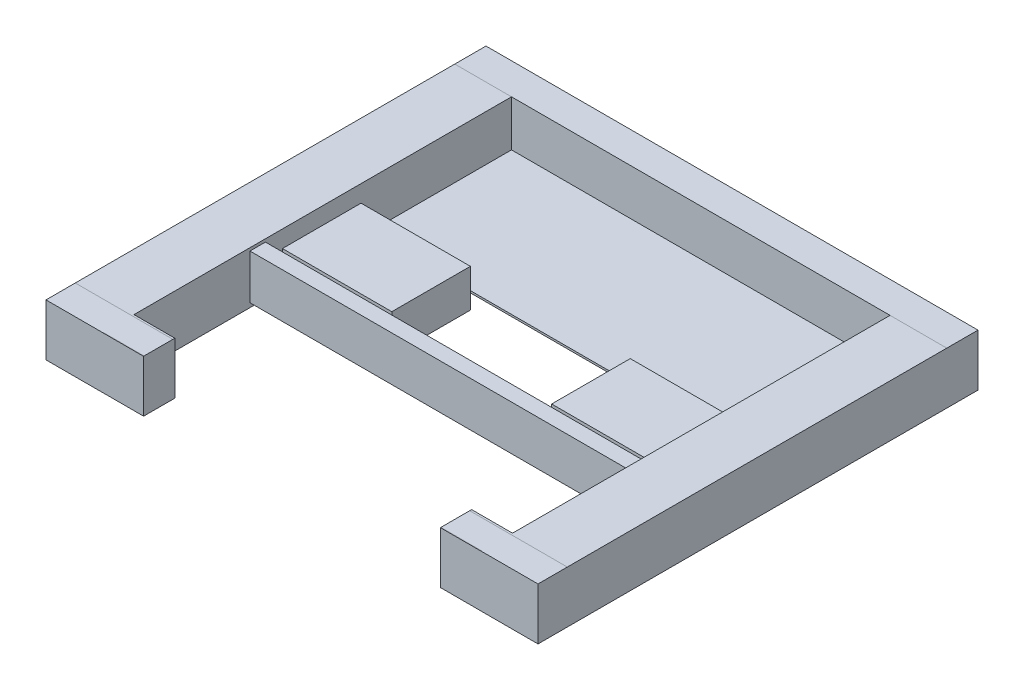
SolidWorks part; units mm, degrees
ref_plane "Front Plane" through (0, 0, 0) normal (0, 0, 1) x (1, 0, 0)
ref_plane "Top Plane" through (0, 0, 0) normal (0, 1, 0) x (1, 0, 0)
ref_plane "Right Plane" through (0, 0, 0) normal (1, 0, 0) x (0, 0, -1)
sketch "Sketch1" plane through (-470.5973, 0, 0) normal (-1, 0, 0) x (0, 0, 1)
  line L0 (375.9827, 96.3326) -> (375.9827, 19.6246) construction
  line L1 (375.9827, 100.2696) -> (375.9827, 15.6876)
  line L2 (328.3577, 100.2696) -> (375.2207, 100.2696) construction
  line L3 (328.3577, 100.2696) -> (375.9827, 100.2696)
  line L4 (375.2207, 15.6876) -> (347.4077, 15.6876) construction
  line L5 (375.9827, 15.6876) -> (347.4077, 15.6876)
  line L6 (-308.1663, 15.4336) -> (-335.9793, 15.4336) construction
  line L7 (-308.1663, 15.4336) -> (-339.9163, 15.4336)
  line L8 (-339.9163, 19.3706) -> (-339.9163, 96.0786) construction
  line L9 (-339.9163, 15.4336) -> (-339.9163, 100.0156)
  line L10 (-335.9793, 100.0156) -> (-289.1163, 100.0156) construction
  line L11 (-339.9163, 100.0156) -> (-289.1163, 100.0156)
  line L12 (-308.1663, 15.4336) -> (347.4077, 15.6876)
  line L13 (-289.1163, 100.0156) -> (328.3577, 100.2696)
extrude "Boss-Extrude1" add sketch "Sketch1" against normal up to surface (92.2881 mm away)
sketch "Sketch2" plane through (-378.3092, 0, 0) normal (1, 0, 0) x (0, 0, -1)
  line L0 (-344.2327, 18.8626) -> (-344.2327, 15.6876) construction
  line L1 (-344.2327, 18.8626) -> (-344.2327, 15.6876)
  line L3 (-325.1827, 100.2696) -> (-375.2207, 100.2696)
  line L4 (-325.1827, 100.2696) -> (-325.1827, 15.6876)
  line L5 (-325.1827, 15.6876) -> (-375.2207, 15.6876)
  line L6 (-375.2207, 100.2696) -> (-375.2207, 15.6876)
  line L8 (289.1163, 100.0156) -> (-328.3577, 100.2696)
  line L9 (-328.3577, 100.2696) -> (-375.9827, 100.2696)
  line L10 (-375.9827, 100.2696) -> (-375.9827, 15.6876)
  line L11 (-375.9827, 15.6876) -> (-347.4077, 15.6876)
  line L12 (-347.4077, 15.6876) -> (308.1663, 15.4336)
  line L13 (308.1663, 15.4336) -> (339.9163, 15.4336)
  line L14 (339.9163, 15.4336) -> (339.9163, 100.0156)
  line L15 (339.9163, 100.0156) -> (289.1163, 100.0156)
  line L16 (289.1163, 100.0156) -> (-328.3577, 100.2696)
  line L17 (-328.3577, 100.2696) -> (-375.9827, 100.2696)
  line L18 (-375.9827, 100.2696) -> (-375.9827, 15.6876)
  line L19 (-375.9827, 15.6876) -> (-347.4077, 15.6876)
  line L20 (-347.4077, 15.6876) -> (308.1663, 15.4336)
  line L21 (308.1663, 15.4336) -> (339.9163, 15.4336)
  line L22 (339.9163, 15.4336) -> (339.9163, 100.0156)
  line L23 (339.9163, 100.0156) -> (289.1163, 100.0156)
  line L26 (-344.2327, 18.8626) -> (-375.2207, 18.8626)
  line L27 (-375.9827, 19.6246) -> (-375.9827, 96.3326)
  line L28 (-375.2207, 97.0946) -> (-325.1827, 97.0946)
  line L29 (-325.1827, 97.0946) -> (-325.1827, 100.2696)
  line L30 (-325.1827, 100.2696) -> (-375.2207, 100.2696)
  line L31 (-379.1577, 96.3326) -> (-379.1577, 19.6246)
  line L32 (-375.2207, 15.6876) -> (-344.2327, 15.6876)
  line L33 (-344.2327, 15.6876) -> (-344.2327, 18.8626)
  line L34 (-344.2327, 18.8626) -> (-375.2207, 18.8626)
  line L35 (-375.9827, 19.6246) -> (-375.9827, 96.3326)
  line L36 (-375.2207, 97.0946) -> (-325.1827, 97.0946)
  line L37 (-325.1827, 97.0946) -> (-325.1827, 100.2696)
  line L38 (-325.1827, 100.2696) -> (-375.2207, 100.2696)
  line L39 (-379.1577, 96.3326) -> (-379.1577, 19.6246)
  line L40 (-375.2207, 15.6876) -> (-344.2327, 15.6876)
  line L41 (-344.2327, 15.6876) -> (-344.2327, 18.8626)
  arc A4 (-375.9827, 19.6246) -> (-375.2207, 18.8626) centre (-375.2207, 19.6246) ccw
  arc A5 (-375.2207, 97.0946) -> (-375.9827, 96.3326) centre (-375.2207, 96.3326) ccw
  arc A6 (-375.2207, 100.2696) -> (-379.1577, 96.3326) centre (-375.2207, 96.3326) ccw
  arc A7 (-379.1577, 19.6246) -> (-375.2207, 15.6876) centre (-375.2207, 19.6246) ccw
  arc A8 (-375.9827, 19.6246) -> (-375.2207, 18.8626) centre (-375.2207, 19.6246) ccw
  arc A9 (-375.2207, 97.0946) -> (-375.9827, 96.3326) centre (-375.2207, 96.3326) ccw
  arc A10 (-375.2207, 100.2696) -> (-379.1577, 96.3326) centre (-375.2207, 96.3326) ccw
  arc A11 (-379.1577, 19.6246) -> (-375.2207, 15.6876) centre (-375.2207, 19.6246) ccw
  line M21 (289.1163, 100.0156) -> (-328.3577, 100.2696)
  line M22 (-328.3577, 100.2696) -> (-375.9827, 100.2696)
  line M23 (-375.9827, 100.2696) -> (-375.9827, 15.6876)
  line M24 (-375.9827, 15.6876) -> (-347.4077, 15.6876)
  dimension "D1" = 0
  dimension "D2" = 0
extrude "Boss-Extrude2" add sketch "Sketch2" along normal up to surface (66.4619 mm away) contours L36 L6 L34 L1 L5 L4 | L6 L36 L4 M21 M22 | L6 A10 L18 A9 | L6 A9 L18 A8 | L1 L34 L6 L5 M24 | A11 L6 A8 M23
ref_plane "Plane1" through (-70.3342, 0, 0) normal (1, 0, 0) x (0, 0, -1)
sketch "Sketch3" plane through (-378.3092, 0, 0) normal (1, 0, 0) x (0, 0, -1)
  line L1 (289.1163, 100.0156) -> (339.9163, 100.0156)
  line L2 (289.1163, 100.0156) -> (289.1163, 15.4336)
  line L3 (289.1163, 15.4336) -> (339.9163, 15.4336)
  line L4 (339.9163, 100.0156) -> (339.9163, 15.4336)
  line L7 (289.1163, 100.0156) -> (-325.1827, 100.2683)
  line L8 (-325.1827, 100.2683) -> (-325.1827, 15.6876)
  line L9 (-325.1827, 15.6876) -> (-347.4077, 15.6876)
  line L10 (-347.4077, 15.6876) -> (308.1663, 15.4336)
  line L11 (308.1663, 15.4336) -> (339.9163, 15.4336)
  line L12 (339.9163, 15.4336) -> (339.9163, 100.0156)
  line L13 (339.9163, 100.0156) -> (289.1163, 100.0156)
  line L14 (289.1163, 100.0156) -> (-325.1827, 100.2683)
  line L15 (-325.1827, 100.2683) -> (-325.1827, 15.6876)
  line L16 (-325.1827, 15.6876) -> (-347.4077, 15.6876)
  line L17 (-347.4077, 15.6876) -> (308.1663, 15.4336)
  line L18 (308.1663, 15.4336) -> (339.9163, 15.4336)
  line L19 (339.9163, 15.4336) -> (339.9163, 100.0156)
  line L20 (339.9163, 100.0156) -> (289.1163, 100.0156)
  line L22 (336.7413, 96.0786) -> (336.7413, 19.3706)
  line L23 (335.9793, 18.6086) -> (308.1663, 18.6086)
  line L24 (308.1663, 18.6086) -> (308.1663, 15.4336)
  line L25 (308.1663, 15.4336) -> (335.9793, 15.4336)
  line L26 (339.9163, 19.3706) -> (339.9163, 96.0786)
  line L27 (335.9793, 100.0156) -> (289.1163, 100.0156)
  line L28 (289.1163, 100.0156) -> (289.1163, 96.8406)
  line L29 (289.1163, 96.8406) -> (335.9793, 96.8406)
  line L30 (336.7413, 96.0786) -> (336.7413, 19.3706)
  line L31 (335.9793, 18.6086) -> (308.1663, 18.6086)
  line L32 (308.1663, 18.6086) -> (308.1663, 15.4336)
  line L33 (308.1663, 15.4336) -> (335.9793, 15.4336)
  line L34 (339.9163, 19.3706) -> (339.9163, 96.0786)
  line L35 (335.9793, 100.0156) -> (289.1163, 100.0156)
  line L36 (289.1163, 100.0156) -> (289.1163, 96.8406)
  line L37 (289.1163, 96.8406) -> (335.9793, 96.8406)
  line L958 (57.3413, 22.0376) -> (336.7413, 22.0376)
  line L959 (336.7413, 22.0376) -> (336.7413, 25.2126)
  line L960 (336.7413, 25.2126) -> (57.3413, 25.2126)
  line L961 (57.3413, 25.2126) -> (57.3413, 22.0376)
  line L962 (57.3413, 22.0376) -> (336.7413, 22.0376)
  line L963 (336.7413, 22.0376) -> (336.7413, 25.2126)
  line L964 (336.7413, 25.2126) -> (57.3413, 25.2126)
  line L965 (57.3413, 25.2126) -> (57.3413, 22.0376)
  arc A4 (335.9793, 18.6086) -> (336.7413, 19.3706) centre (335.9793, 19.3706) ccw
  arc A5 (335.9793, 15.4336) -> (339.9163, 19.3706) centre (335.9793, 19.3706) ccw
  arc A6 (339.9163, 96.0786) -> (335.9793, 100.0156) centre (335.9793, 96.0786) ccw
  arc A7 (336.7413, 96.0786) -> (335.9793, 96.8406) centre (335.9793, 96.0786) ccw
  arc A8 (335.9793, 18.6086) -> (336.7413, 19.3706) centre (335.9793, 19.3706) ccw
  arc A9 (335.9793, 15.4336) -> (339.9163, 19.3706) centre (335.9793, 19.3706) ccw
  arc A10 (339.9163, 96.0786) -> (335.9793, 100.0156) centre (335.9793, 96.0786) ccw
  arc A11 (336.7413, 96.0786) -> (335.9793, 96.8406) centre (335.9793, 96.0786) ccw
  line M23 (-347.4077, 15.6876) -> (308.1663, 15.4336)
  line M24 (308.1663, 15.4336) -> (339.9163, 15.4336)
  line M25 (339.9163, 15.4336) -> (339.9163, 100.0156)
  line M26 (339.9163, 100.0156) -> (289.1163, 100.0156)
  dimension "D1" = 0
  dimension "D2" = 0
  dimension "D3" = 0
extrude "Boss-Extrude3" add sketch "Sketch3" along normal up to surface (307.975 mm away) contours L30 A11 L37 L2 L32 L31 A8 M23 | A11 L30 A8 L31 L32 A9 L19 A10 L20 L2 L37 M24 | A10 M25 M26 | A9 L18 M25 | L30 A11 L37 L2 L964 | L30 L964 L2 L962 | L964 L965 L962 L2
sketch "Sketch4" plane through (-378.3092, 0, 0) normal (1, 0, 0) x (0, 0, -1)
  line L1 (-83.5558, 72.5361) -> (44.3144, 72.5361)
  line L2 (-83.5558, 72.5361) -> (-83.5558, 10.7821)
  line L3 (-83.5558, 10.7821) -> (44.3144, 10.7821)
  line L4 (44.3144, 72.5361) -> (44.3144, 10.7821)
  line L9 (289.1163, 25.2126) -> (289.1163, 100.0156)
  line L10 (289.1163, 100.0156) -> (-325.1827, 100.2683)
  line L11 (-325.1827, 100.2683) -> (-325.1827, 15.6876)
  line L12 (-325.1827, 15.6876) -> (-347.4077, 15.6876)
  line L13 (-347.4077, 15.6876) -> (289.1163, 15.441)
  line L14 (289.1163, 15.441) -> (289.1163, 22.0376)
  line L15 (289.1163, 22.0376) -> (57.3413, 22.0376)
  line L16 (57.3413, 22.0376) -> (57.3413, 25.2126)
  line L17 (57.3413, 25.2126) -> (289.1163, 25.2126)
  line L18 (289.1163, 25.2126) -> (289.1163, 100.0156)
  line L19 (289.1163, 100.0156) -> (-325.1827, 100.2683)
  line L20 (-325.1827, 100.2683) -> (-325.1827, 15.6876)
  line L21 (-325.1827, 15.6876) -> (-347.4077, 15.6876)
  line L22 (-347.4077, 15.6876) -> (289.1163, 15.441)
  line L23 (289.1163, 15.441) -> (289.1163, 22.0376)
  line L24 (289.1163, 22.0376) -> (57.3413, 22.0376)
  line L25 (57.3413, 22.0376) -> (57.3413, 25.2126)
  line L26 (57.3413, 25.2126) -> (289.1163, 25.2126)
  arc A0 (-22.8539, 49.6506) -> (-82.5037, 33.6675) centre (-52.6788, 41.6591) ccw construction
  arc A1 (-82.5037, 33.6675) -> (-22.8539, 49.6506) centre (-52.6788, 41.6591) ccw construction
  arc A2 (-16.3875, 49.6506) -> (43.2623, 33.6675) centre (13.4374, 41.6591) ccw construction
  arc A3 (43.2623, 33.6675) -> (-16.3875, 49.6506) centre (13.4374, 41.6591) ccw construction
  arc A4 (-22.8539, 49.6506) -> (-82.5037, 33.6675) centre (-52.6788, 41.6591) ccw
  arc A5 (-82.5037, 33.6675) -> (-22.8539, 49.6506) centre (-52.6788, 41.6591) ccw
  arc A6 (-16.3875, 49.6506) -> (43.2623, 33.6675) centre (13.4374, 41.6591) ccw
  arc A7 (43.2623, 33.6675) -> (-16.3875, 49.6506) centre (13.4374, 41.6591) ccw
  line M18 (-347.4077, 15.6876) -> (289.1163, 15.441)
  dimension "D1" = 0
extrude "Boss-Extrude4" add sketch "Sketch4" along normal up to surface (177.926 mm away) contours A7 A6 L22 | A4 A5 L22 | A7 L1 A4 A5 A6 M18 | L22 A5 | A6 A5 L3 M18 | L22 A6 | A6 L3 L4 M18 | A5 L2 L3 M18 | A5 A4 L2 M18 | A4 L1 L2 | A7 L4 L1 | A7 A6 L4 M18
sketch "Sketch6" plane through (-378.3092, 0, 0) normal (1, 0, 0) x (0, 0, -1)
  line L1 (-136.4295, 95.4857) -> (-111.2814, 95.4857)
  line L2 (-136.4295, 95.4857) -> (-136.4295, 22.6149)
  line L3 (-136.4295, 22.6149) -> (-111.2814, 22.6149)
  line L4 (-111.2814, 95.4857) -> (-111.2814, 22.6149)
extrude "Boss-Extrude5" add sketch "Sketch6" along normal up to surface (307.975 mm away) up to face at (-70.3342, 37.8711, -251.0163)
mirror "Mirror1" about plane through (-70.3342, 0, 0) normal (1, 0, 0) of bodies 106 104
